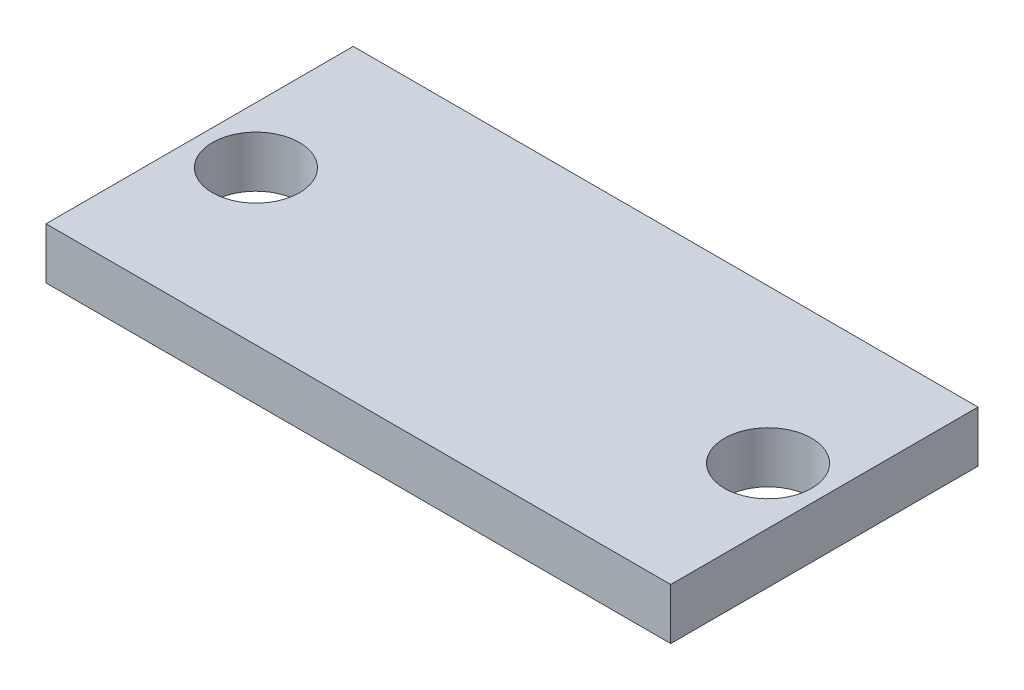
SolidWorks part; units mm, degrees
ref_plane "Alzado" through (0, 0, 0) normal (0, 0, 1) x (1, 0, 0)
ref_plane "Planta" through (0, 0, 0) normal (0, 1, 0) x (1, 0, 0)
ref_plane "Vista lateral" through (0, 0, 0) normal (1, 0, 0) x (0, 0, -1)
sketch "Croquis1" plane through (0, 0, 0) normal (0, 1, 0) x (1, 0, 0)
  line L0 (0, -16.4018) -> (0, 78.9163) construction
  line L1 (-63.9099, 0) -> (63.9099, 0) construction
  line L2 (-8.0467, 6) -> (8.0467, 6)
  line L3 (8.0467, 6) -> (8.0467, 2.4617)
  line L4 (-8.0467, -6) -> (8.0467, -6)
  line L5 (8.0467, -6) -> (8.0467, -2.4617)
  line L6 (-8.0467, -6) -> (-8.0467, -2.4617)
  line L7 (-8.0467, 6) -> (-8.0467, 2.4617)
  line L8 (8.0467, -2.4617) -> (8.0467, 2.4617)
  line L9 (-8.0467, -2.4617) -> (-8.0467, 2.4617)
  line L11 (8.0467, 6) -> (12.2, 6)
  line L12 (8.0467, 6) -> (8.0467, -6)
  line L13 (8.0467, -6) -> (12.2, -6)
  line L14 (12.2, 6) -> (12.2, -6)
  line L15 (-8.0467, 6) -> (-12.2, 6)
  line L16 (-8.0467, 6) -> (-8.0467, -6)
  line L17 (-8.0467, -6) -> (-12.2, -6)
  line L18 (-12.2, 6) -> (-12.2, -6)
  circle A0 centre (10, 0) radius 1.7
  arc A1 (9.6576, -2.1732) -> (9.6576, 2.1732) centre (10, 0) ccw
  arc A2 (8.0467, 2.4617) -> (9.6576, 2.1732) centre (9.2686, 4.6427) ccw
  arc A3 (8.0467, -2.4617) -> (9.6576, -2.1732) centre (9.2686, -4.6427) cw
  arc A4 (-8.0467, -2.4617) -> (-9.6576, -2.1732) centre (-9.2686, -4.6427) ccw
  arc A5 (-8.0467, 2.4617) -> (-9.6576, 2.1732) centre (-9.2686, 4.6427) cw
  arc A6 (-9.6576, -2.1732) -> (-9.6576, 2.1732) centre (-10, 0) cw
  circle A7 centre (-10, 0) radius 1.7
  point P6 (7.8, 0)
  point P10 (8, 0)
  point P19 (0, 0)
  point P28 (0, -6)
  point P29 (-8, 0)
  point P30 (0, 6)
  dimension "D1" = 7.8
  dimension "D5" = 3.4
  dimension "D6" = 5
  dimension "D3" = 10
  dimension "D2" = 2.2
  dimension "D4" = 6
  dimension "D7" = 1.6366
  dimension "D8" = 2.2
extrude "Saliente-Extruir1" add sketch "Croquis1" along normal blind 2 contours L9 L6 L4 L5 L8 L3 L2 L7 | L8 A3 A1 A2 A0 | A6 A4 L9 A5 A7 | A4 A6 L18 L17 L6 | L18 A6 A5 L7 L15 | L3 A2 A1 L14 L11 | A3 L5 L13 L14 A1
ref_plane "Plano1" through (3.25, 0, 0) normal (1, 0, 0) x (0, 0, -1)
sketch "Croquis4" plane through (3.25, 0, 0) normal (1, 0, 0) x (0, 0, -1)
  line L0 (-6, 2) -> (-4, 2)
  line L1 (-6, 2) -> (-5.1, 2.9)
  line L2 (-5, 3) -> (-5, 2) construction
  line L3 (-4, 2) -> (-4.9, 2.9)
  line L4 (-5.1, 2.9) -> (-4.9, 2.9)
  dimension "D1" = 1
  dimension "D2" = 1
  dimension "D3" = 0.9
sketch "Sketch1" plane through (0, 0, 6) normal (0, 0, 1) x (1, 0, 0)
  line L0 (0, 2) -> (0, 0)
  line L1 (-8.0467, 2) -> (8.0467, 2) construction
  line L4 (-1, 2) -> (1, 2)
  line L5 (-1, 2) -> (-1, 0)
  line L6 (-1, 0) -> (1, 0)
  line L7 (1, 2) -> (1, 0)
  dimension "D1" = 1
  dimension "D2" = 1
